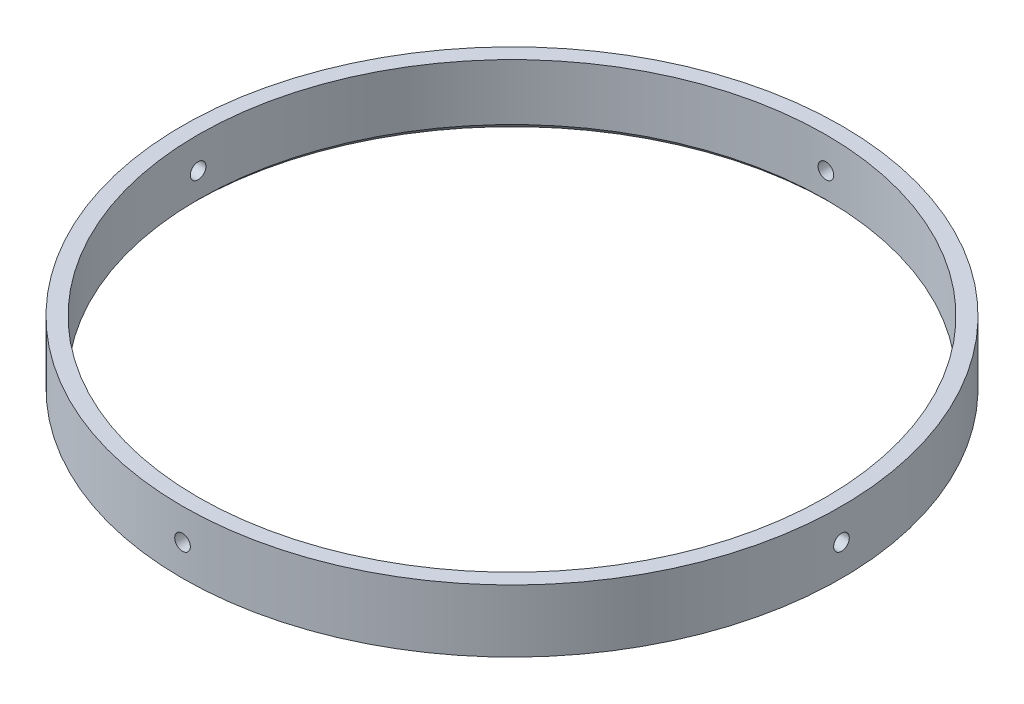
SolidWorks part; units mm, degrees
ref_plane "Front Plane" through (0, 0, 0) normal (0, 0, 1) x (1, 0, 0)
ref_plane "Top Plane" through (0, 0, 0) normal (0, 1, 0) x (1, 0, 0)
ref_plane "Right Plane" through (0, 0, 0) normal (1, 0, 0) x (0, 0, -1)
sketch "Sketch1" plane through (0, 0, 0) normal (0, 1, 0) x (1, 0, 0)
  circle A0 centre (0, 0) radius 66.9925
  circle A1 centre (0, 0) radius 63.8175
  dimension "D1" = 127.635
  dimension "D2" = 3.175
extrude "Boss-Extrude1" add sketch "Sketch1" along normal blind 12.7
sketch "Sketch2" plane through (0, 0, 0) normal (0, 0, 1) x (1, 0, 0)
  line L0 (0, 0) -> (0, 12.7) construction
  line L1 (63.8175, 12.7) -> (-63.8175, 12.7) construction
  circle A0 centre (0, 6.35) radius 1.5875
  dimension "D1" = 3.175
extrude "Cut-Extrude1" cut sketch "Sketch2" against normal up to surface (66.9737 mm away)
pattern_circular "CirPattern1" count 4 over 360 about axis through (0, 12.7, 0) along (0, -1, 0) of "Cut-Extrude1"
chamfer "Chamfer1" distance 1.27 angle 45 1 edges at (0, 0, 63.8175)
